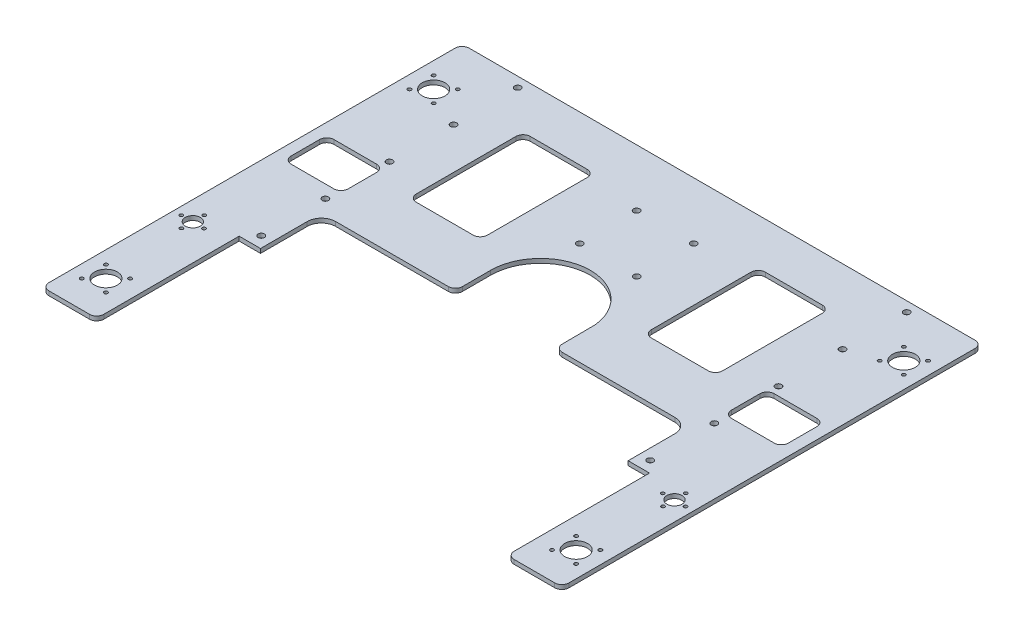
SolidWorks part; units mm, degrees
ref_plane "Front Plane" through (0, 0, 0) normal (0, 0, 1) x (1, 0, 0)
ref_plane "Top Plane" through (0, 0, 0) normal (0, 1, 0) x (1, 0, 0)
ref_plane "Right Plane" through (0, 0, 0) normal (1, 0, 0) x (0, 0, -1)
sketch "Sketch1" plane through (0, 0, 0) normal (0, 1, 0) x (1, 0, 0)
  line L1 (182.5, -185) -> (-182.5, -185)
  line L2 (182.5, -185) -> (182.5, 185)
  line L3 (182.5, 185) -> (-182.5, 185)
  line L4 (-182.5, -185) -> (-182.5, 185)
  line L5 (182.5, -185) -> (-182.5, 185) construction
  line L6 (182.5, 185) -> (-182.5, -185) construction
  point P0 (0, 0)
  dimension "D1" = 365
  dimension "D2" = 370
extrude "Boss-Extrude1" add sketch "Sketch1" along normal blind 3
sketch "Sketch2" plane through (0, 3, 0) normal (0, 1, 0) x (1, 0, 0)
  line L0 (-182.5, 185) -> (-182.5, -185) construction
  line L1 (182.5, -185) -> (-182.5, -185)
  line L2 (182.5, -185) -> (182.5, -50)
  line L3 (182.5, -50) -> (-182.5, -50)
  line L4 (-182.5, -185) -> (-182.5, -50)
  dimension "D1" = 135
extrude "Cut-Extrude1" cut sketch "Sketch2" against normal blind 10
sketch "Sketch3" plane through (0, 3, 0) normal (0, 1, 0) x (1, 0, 0)
  circle A0 centre (-173.4853, 155.9853) radius 1.25
  circle A1 centre (-173.4853, 139.0147) radius 1.25
  circle A2 centre (-156.5147, 155.9853) radius 1.25
  circle A3 centre (-156.5147, 139.0147) radius 1.25
  circle A4 centre (-165, 147.5) radius 8
  circle A5 centre (156.5147, 155.9853) radius 1.25
  circle A6 centre (173.4853, 155.9853) radius 1.25
  circle A7 centre (173.4853, 139.0147) radius 1.25
  circle A8 centre (156.5147, 139.0147) radius 1.25
  circle A9 centre (165, 147.5) radius 8
extrude "Cut-Extrude2" cut sketch "Sketch3" against normal blind 10
sketch "Sketch4" plane through (0, 3, 0) normal (0, 1, 0) x (1, 0, 0)
  circle A0 centre (-169, -17.5) radius 5.3
  circle A1 centre (-169, -9.5) radius 1.2
  circle A2 centre (-169, -25.5) radius 1.2
  circle A3 centre (-161, -17.6741) radius 1.2
  circle A4 centre (-177, -17.6741) radius 1.2
  dimension "D1" = 8
  dimension "D2" = 8
  dimension "D4" = 8
  dimension "D3" = 8
extrude "Cut-Extrude3" cut sketch "Sketch4" against normal blind 10
mirror "Mirror1" about plane through (0, 0, 0) normal (1, 0, 0) of "Cut-Extrude3"
sketch "Sketch5" plane through (0, 3, 0) normal (0, 1, 0) x (1, 0, 0)
  line L0 (182.5, -50) -> (-182.5, -50) construction
  line L1 (-129, -50) -> (129, -50)
  line L2 (-129, -50) -> (-129, 32.7698)
  line L3 (-129, 32.7698) -> (129, 32.7698)
  line L4 (129, -50) -> (129, 32.7698)
  line L5 (-182.5, 185) -> (-182.5, -50) construction
  line L6 (182.5, -50) -> (182.5, 185) construction
  dimension "D1" = 53.5
  dimension "D2" = 53.5
extrude "Cut-Extrude4" cut sketch "Sketch5" against normal blind 10
sketch "Sketch6" plane through (0, 3, 0) normal (0, 1, 0) x (1, 0, 0)
  line L0 (-144, -94.5949) -> (-144, 67.8711) construction
  line L1 (-129, -50) -> (-144, -50)
  line L2 (-129, -50) -> (-129, -10)
  line L3 (-129, -10) -> (-144, -10)
  line L4 (-144, -50) -> (-144, -10)
  dimension "D1" = 40
extrude "Cut-Extrude5" cut sketch "Sketch6" against normal blind 10
mirror "Mirror2" about plane through (0, 0, 0) normal (1, 0, 0) of "Cut-Extrude5"
sketch "Sketch7" plane through (0, 3, 0) normal (0, 1, 0) x (1, 0, 0)
  line L0 (-35, 57.5) -> (-35, 32.7698)
  line L1 (129, 32.7698) -> (-129, 32.7698) construction
  line L2 (-35, 32.7698) -> (35, 32.7698)
  line L3 (35, 32.7698) -> (34.8086, 61.1549)
  circle A0 centre (0, 57.5) radius 35
  line M32 (-129, 32.7698) -> (129, 32.7698)
extrude "Cut-Extrude6" cut sketch "Sketch7" against normal blind 10 contours A0 L0 M32 | L2 A0 L3 | A0 L3 M32
sketch "Sketch8" plane through (0, 3, 0) normal (0, 1, 0) x (1, 0, 0)
  line L0 (182.5, 185) -> (-182.5, 185) construction
  line L1 (-169.5, 52) -> (-139.5, 52)
  line L2 (-174.5, 57) -> (-174.5, 77)
  line L3 (-169.5, 82) -> (-139.5, 82)
  line L4 (-134.5, 57) -> (-134.5, 77)
  line L5 (-182.5, 185) -> (-182.5, -50) construction
  arc A0 (-169.5, 82) -> (-174.5, 77) centre (-169.5, 77) ccw
  arc A1 (-169.5, 52) -> (-174.5, 57) centre (-169.5, 57) cw
  arc A2 (-139.5, 52) -> (-134.5, 57) centre (-139.5, 57) ccw
  arc A3 (-134.5, 77) -> (-139.5, 82) centre (-139.5, 77) ccw
  point P4 (-174.5, 67)
  point P13 (-174.5, 52)
  point P16 (-134.5, 52)
  point P19 (-134.5, 82)
  dimension "D5" = 5
  dimension "D1" = 40
  dimension "D2" = 30
  dimension "D3" = 118
  dimension "D4" = 8
extrude "Cut-Extrude7" cut sketch "Sketch8" against normal blind 10
mirror "Mirror3" about plane through (0, 0, 0) normal (1, 0, 0) of "Cut-Extrude7"
sketch "Sketch9" plane through (0, 3, 0) normal (0, 1, 0) x (1, 0, 0)
  line L0 (-129, -10) -> (-144, -10) construction
  line L1 (0, -1.65) -> (0, 1.65) construction
  circle A0 centre (-136.5, -2) radius 2.2
  circle A1 centre (-136.5, 43) radius 2.2
  circle A2 centre (-136.5, 88) radius 2.2
  circle A3 centre (-136.5, 133) radius 2.2
  circle A4 centre (-136.5, 178) radius 2.2
  circle A5 centre (136.5, 178) radius 2.2
  circle A6 centre (136.5, 133) radius 2.2
  circle A7 centre (136.5, 88) radius 2.2
  circle A8 centre (136.5, 43) radius 2.2
  circle A9 centre (136.5, -2) radius 2.2
  dimension "D1" = 8
  dimension "D2" = 5
extrude "Cut-Extrude8" cut sketch "Sketch9" against normal blind 10
fillet "Fillet1" radius 10 2 edges at (129, 1.5, -32.7698) (-129, 1.5, -32.7698)
sketch "Sketch10" plane through (0, 3, 0) normal (0, 1, 0) x (1, 0, 0)
  line L0 (119, 32.7698) -> (35, 32.7698) construction
  line L1 (102.5, 72.7698) -> (62.5, 72.7698)
  line L2 (107.5, 77.7698) -> (107.5, 147.7698)
  line L3 (102.5, 152.7698) -> (62.5, 152.7698)
  line L4 (57.5, 77.7698) -> (57.5, 147.7698)
  line L5 (107.5, 72.7698) -> (57.5, 152.7698) construction
  line L6 (107.5, 152.7698) -> (57.5, 72.7698) construction
  line L7 (182.5, -50) -> (182.5, 185) construction
  line L8 (0, -1.65) -> (0, 1.65) construction
  line L9 (-107.5, 152.7698) -> (-57.5, 72.7698) construction
  line L10 (-107.5, 72.7698) -> (-57.5, 152.7698) construction
  line L11 (-57.5, 77.7698) -> (-57.5, 147.7698)
  line L12 (-102.5, 152.7698) -> (-62.5, 152.7698)
  line L13 (-107.5, 77.7698) -> (-107.5, 147.7698)
  line L14 (-102.5, 72.7698) -> (-62.5, 72.7698)
  arc A0 (57.5, 77.7698) -> (62.5, 72.7698) centre (62.5, 77.7698) ccw
  arc A1 (107.5, 77.7698) -> (102.5, 72.7698) centre (102.5, 77.7698) cw
  arc A2 (107.5, 147.7698) -> (102.5, 152.7698) centre (102.5, 147.7698) ccw
  arc A3 (62.5, 152.7698) -> (57.5, 147.7698) centre (62.5, 147.7698) ccw
  arc A4 (-62.5, 152.7698) -> (-57.5, 147.7698) centre (-62.5, 147.7698) cw
  arc A5 (-107.5, 147.7698) -> (-102.5, 152.7698) centre (-102.5, 147.7698) cw
  arc A6 (-107.5, 77.7698) -> (-102.5, 72.7698) centre (-102.5, 77.7698) ccw
  arc A7 (-57.5, 77.7698) -> (-62.5, 72.7698) centre (-62.5, 77.7698) cw
  point P0 (82.5, 112.7698)
  point P39 (-82.5, 112.7698)
  dimension "D5" = 5
  dimension "D1" = 50
  dimension "D2" = 80
  dimension "D3" = 80
  dimension "D4" = 100
extrude "Cut-Extrude9" cut sketch "Sketch10" against normal blind 10
sketch "Sketch11" plane through (0, 3, 0) normal (0, 1, 0) x (1, 0, 0)
  line L0 (182.5, 185) -> (-182.5, 185) construction
  line L1 (0, -1.65) -> (0, 1.65) construction
  circle A0 centre (20, 145) radius 2.2
  circle A1 centre (20, 105) radius 2.2
  circle A2 centre (-20, 105) radius 2.2
  circle A3 centre (-20, 145) radius 2.2
  point P6 (0, 185)
  dimension "D1" = 40
  dimension "D2" = 20
  dimension "D3" = 40
extrude "Cut-Extrude10" cut sketch "Sketch11" against normal blind 10
sketch "Sketch12" plane through (0, 3, 0) normal (0, 1, 0) x (1, 0, 0)
  line L0 (-144, -10) -> (-144, -50) construction
  line L1 (-182.5, -50) -> (-144, -50)
  line L2 (-182.5, -50) -> (-182.5, -110)
  line L3 (-182.5, -110) -> (-144, -110)
  line L4 (-144, -50) -> (-144, -110)
  dimension "D1" = 0
  dimension "D2" = 60
extrude "Boss-Extrude2" add sketch "Sketch12" against normal blind 3
mirror "Mirror4" about plane through (0, 0, 0) normal (1, 0, 0) of "Boss-Extrude2"
pattern_linear "LPattern1" count 2 spacing 230 along (0, 0, 1) of "Cut-Extrude2"
fillet "Fillet2" radius 5 8 edges at (35, 1.5, -32.7698) (-35, 1.5, -32.7698) (144, 1.5, 110) (182.5, 1.5, 110) (-144, 1.5, 110) (-182.5, 1.5, 110) (-182.5, 1.5, -185) (182.5, 1.5, -185)
